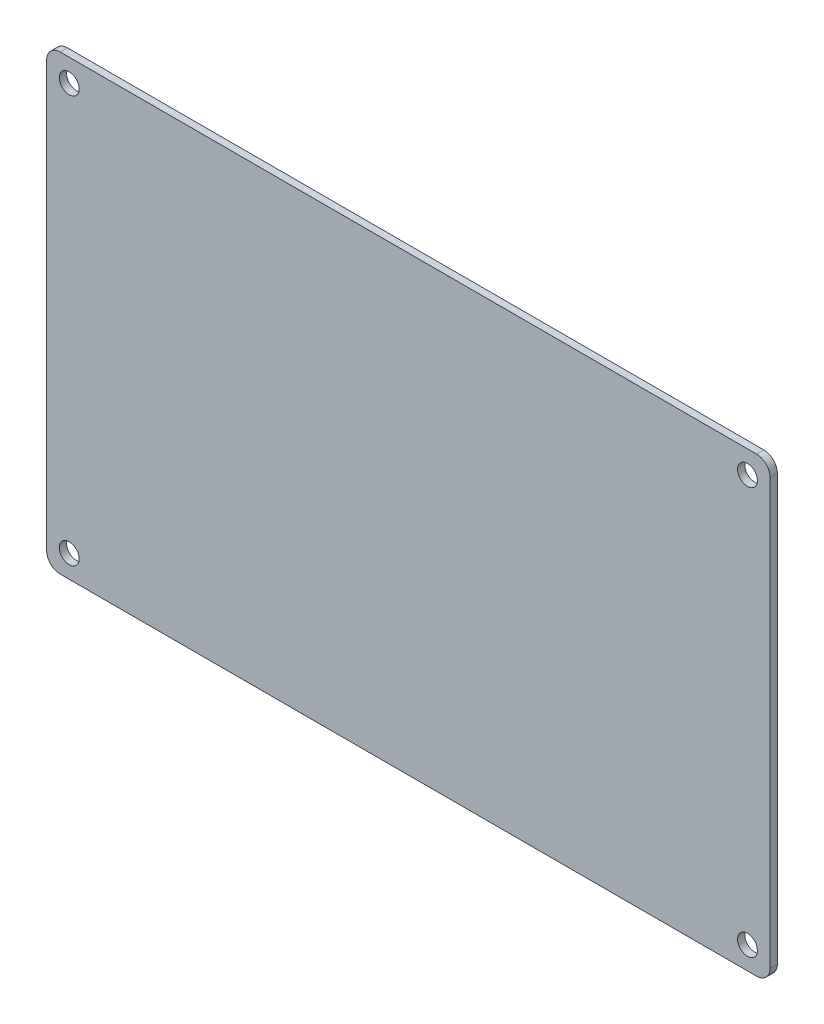
SolidWorks part; units mm, degrees
ref_plane "正面" through (0, 0, 0) normal (0, 0, 1) x (1, 0, 0)
ref_plane "平面" through (0, 0, 0) normal (0, 1, 0) x (1, 0, 0)
ref_plane "右側面" through (0, 0, 0) normal (1, 0, 0) x (0, 0, -1)
sketch "ｽｹｯﾁ1" plane through (0, 0, 0) normal (0, 0, 1) x (1, 0, 0)
  line L1 (80, -50) -> (-80, -50)
  line L2 (80, -50) -> (80, 50)
  line L3 (80, 50) -> (-80, 50)
  line L4 (-80, -50) -> (-80, 50)
  line L5 (80, -50) -> (-80, 50) construction
  line L6 (80, 50) -> (-80, -50) construction
  point P0 (0, 0)
  dimension "D1" = 100
  dimension "D2" = 160
extrude "ﾎﾞｽ - 押し出し1" add sketch "ｽｹｯﾁ1" along normal blind 1.6
fillet "ﾌｨﾚｯﾄ1" radius 3 4 edges at (80, -50, 0.8) (-80, -50, 0.8) (-80, 50, 0.8) (80, 50, 0.8)
sketch "ｽｹｯﾁ2" plane through (0, 0, 1.6) normal (0, 0, 1) x (1, 0, 0)
  line L1 (75, -45) -> (-75, -45)
  line L2 (75, -45) -> (75, 45)
  line L3 (75, 45) -> (-75, 45)
  line L4 (-75, -45) -> (-75, 45)
  line L5 (75, -45) -> (-75, 45) construction
  line L6 (75, 45) -> (-75, -45) construction
  point P0 (0, 0)
  dimension "D1" = 90
  dimension "D2" = 150
hole_wizard "M3 すきま穴1" positions "ｽｹｯﾁ3" profile "ｽｹｯﾁ4" hole size "M3" standard "ISO"
sketch "ｽｹｯﾁ3" plane through (0, 0, 1.6) normal (0, 0, 1) x (1, 0, 0)
  point P0 (-75, -45)
  point P3 (-75, 45)
  point P6 (75, 45)
  point P9 (75, -45)
sketch "ｽｹｯﾁ4" plane through (-75, -45, 1.6) normal (1, 0, 0) x (0, -1, 0)
  line L0 (0, 0) -> (0, 6)
  line L1 (0, 6) -> (2.2, 6)
  line L2 (2.2, 6) -> (2.2, 0)
  line L5 (2.2, 0) -> (0, 0)
  line L10 (0, 6) -> (-2.2, 6) construction
  line L11 (0, -6.35) -> (0, 107.95) construction
  dimension "穴の直径" = 4.4
  dimension "穴の深さ" = 6
  dimension "ﾄﾞﾘﾙ角度" = 180
